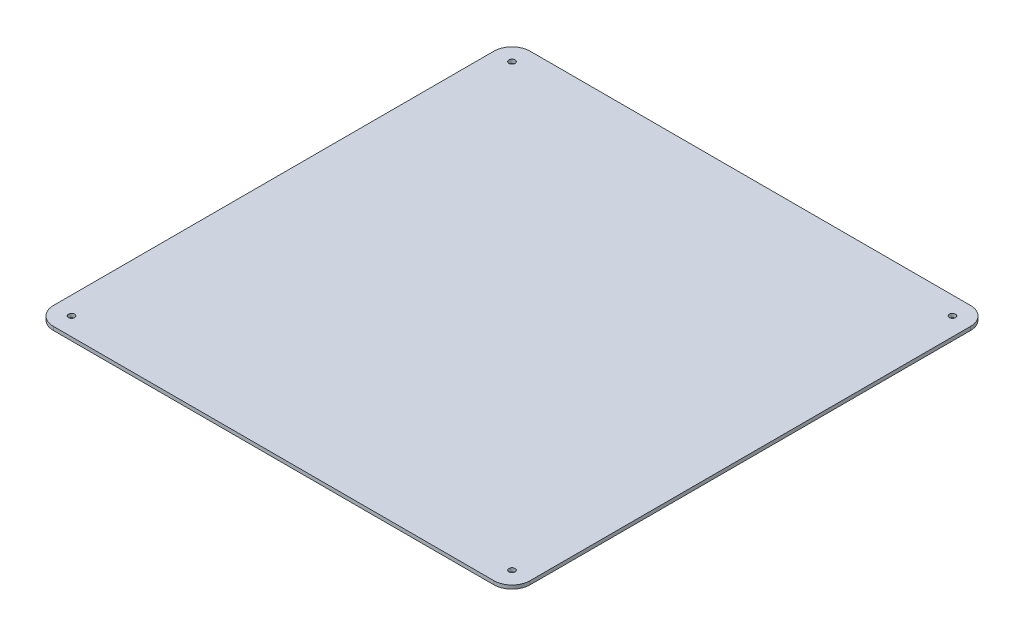
SolidWorks part; units mm, degrees
ref_plane "Front Plane" through (0, 0, 0) normal (0, 0, 1) x (1, 0, 0)
ref_plane "Top Plane" through (0, 0, 0) normal (0, 1, 0) x (1, 0, 0)
ref_plane "Right Plane" through (0, 0, 0) normal (1, 0, 0) x (0, 0, -1)
sketch "Sketch1" plane through (0, 0, 0) normal (0, 1, 0) x (1, 0, 0)
  line L1 (-197.5, 197.5) -> (197.5, 197.5)
  line L2 (-197.5, 197.5) -> (-197.5, -197.5)
  line L3 (-197.5, -197.5) -> (197.5, -197.5)
  line L4 (197.5, 197.5) -> (197.5, -197.5)
  line L5 (-197.5, 197.5) -> (197.5, -197.5) construction
  line L6 (-197.5, -197.5) -> (197.5, 197.5) construction
  circle A0 centre (-182.5, 182.5) radius 2.55
  circle A1 centre (182.5, 182.5) radius 2.55
  circle A2 centre (182.5, -182.5) radius 2.55
  circle A3 centre (-182.5, -182.5) radius 2.55
  point P0 (0, 0)
  dimension "D4" = 5.1
  dimension "D6" = 5.1
  dimension "D8" = 5.1
  dimension "D10" = 5.1
  dimension "D1" = 395
  dimension "D2" = 395
  dimension "D3" = 15
  dimension "D5" = 15
  dimension "D7" = 15
  dimension "D9" = 15
extrude "Boss-Extrude1" add sketch "Sketch1" along normal blind 3
fillet "Fillet1" radius 15 4 edges at (-197.5, 1.5, -197.5) (197.5, 1.5, -197.5) (197.5, 1.5, 197.5) (-197.5, 1.5, 197.5)
